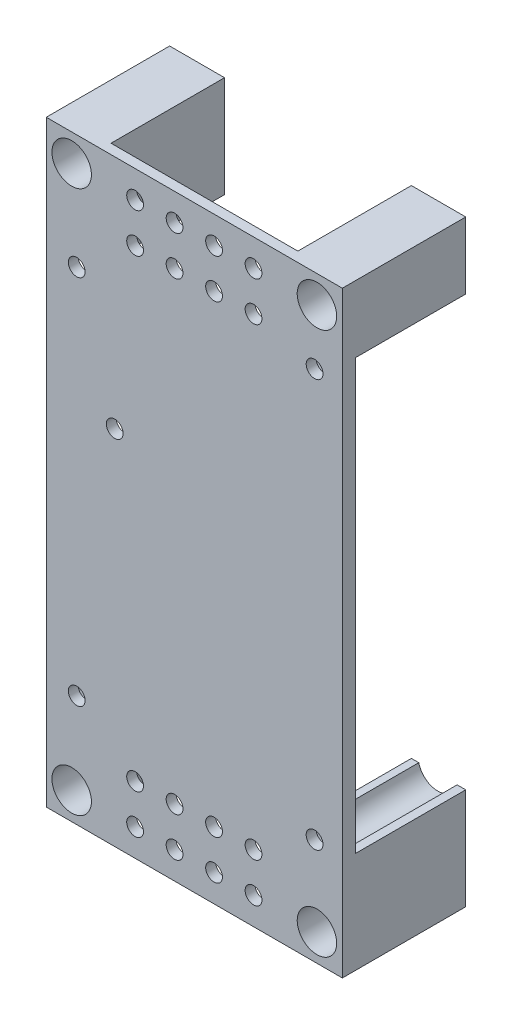
SolidWorks part; units mm, degrees
ref_plane "Plan de face" through (0, 0, 0) normal (0, 0, 1) x (1, 0, 0)
ref_plane "Plan de dessus" through (0, 0, 0) normal (0, 1, 0) x (1, 0, 0)
ref_plane "Plan de droite" through (0, 0, 0) normal (1, 0, 0) x (0, 0, -1)
sketch "Esquisse1" plane through (0, 0, 0) normal (0, 0, 1) x (1, 0, 0)
  line L5 (0.9187, 44.8704) -> (16.1486, 44.8704) construction
  line L8 (-13.8839, 67.0531) -> (-13.8839, -53.9979) construction
  line L9 (-43.8839, 67.0531) -> (16.1161, 67.0531)
  line L10 (-43.8839, 67.0531) -> (-43.8839, -53.9979)
  line L11 (-43.8839, -53.9979) -> (16.1161, -53.9979)
  line L12 (16.1161, 67.0531) -> (16.1161, -53.9979)
  line L13 (-43.8839, 6.5276) -> (16.1161, 6.5276) construction
  line L14 (-52.5801, -48.4724) -> (36.6857, -48.4724) construction
  line L15 (-38.8839, -50.2856) -> (-38.8839, -32.7452) construction
  circle A5 centre (-38.7333, -48.4724) radius 4
  circle A6 centre (10.9655, -48.4724) radius 4
  circle A7 centre (10.9655, 61.5276) radius 4
  circle A8 centre (-38.7333, 61.5276) radius 4
  line B0 (-37.7133, -31.3924) -> (-37.7133, 63.6939) construction
  line B1 (-37.7133, -31.3924) -> (13.3877, -31.3924) construction
  line B2 (-37.7133, 43.8476) -> (13.7913, 43.8476) construction
  line B3 (10.4867, 62.1293) -> (-37.7133, 62.1293) construction
  line B4 (10.4867, -32.5324) -> (10.4867, 66.0242) construction
  line B5 (3.5231, 50.0676) -> (21.137, 50.0676) construction
  line B6 (-13.6133, 62.1293) -> (-13.6133, 58.5502) construction
  line B7 (-48.2733, 19.324) -> (4.9867, 19.324) construction
  line B8 (-43.1133, 8.2967) -> (15.8867, 8.2967) construction
  circle B9 centre (10.4867, -32.5324) radius 1.7
  circle B10 centre (10.4867, 50.0676) radius 1.7
  circle B11 centre (-30.0133, 19.324) radius 1.7
  circle B12 centre (-37.7133, -31.3924) radius 1.7
  circle B13 centre (-37.7133, 43.8476) radius 1.7
  dimension "D4" = 60
  dimension "D5" = 17.08
  dimension "D1" = 55
  dimension "D2" = 121.051
  dimension "D3" = 25
  dimension "D6" = 1.02
sketch_block_instance "Bloc2-1"
sketch_block "Bloc2" parameters "D5"=4, "D1"=75.24, "D2"=48.2, "D3"=6.22, "D4"=1.14
extrude "Boss.-Extru.1" add sketch "Esquisse1" along normal blind 25
sketch "Esquisse2" plane through (16.1161, 0, 0) normal (1, 0, 0) x (0, 0, -1)
  line L0 (-25, 6.5276) -> (0, 6.5276) construction
  line L1 (-25, -53.9979) -> (-25, 67.0531) construction
  line L2 (0, -53.9979) -> (0, 67.0531) construction
  line L3 (-22.3, -67.4787) -> (-22.3, 79.6794) construction
  line L4 (-25, -33.4724) -> (0, -33.4724) construction
  line L5 (0, -33.4724) -> (-22.3, -33.4724)
  line L6 (-22.3, -33.4724) -> (-22.3, 46.5276)
  line L7 (0, -33.4724) -> (0, 46.5276) construction
  line L8 (0, 46.5276) -> (-22.3, 46.5276)
  point P14 (-22.3, 6.5276)
  dimension "D1" = 22.3
  dimension "D2" = 40
extrude "Enlèv. mat.-Extru.1" cut sketch "Esquisse2" against normal through all and the other way through all
sketch "Esquisse3" plane through (0, 0, 0) normal (0, 0, -1) x (-1, 0, 0)
  circle A0 centre (-10.4867, -32.5324) radius 4
  circle A1 centre (37.7133, -31.3924) radius 4
  circle A2 centre (-10.4867, 50.0676) radius 4
  circle A3 centre (37.7133, 43.8476) radius 4
extrude "Enlèv. mat.-Extru.2" cut sketch "Esquisse3" against normal blind 23
sketch "Esquisse4" plane through (0, -53.9979, 0) normal (0, -1, 0) x (1, 0, 0)
  line L1 (-32.76, 23) -> (5.0976, 23)
  line L2 (-32.76, 23) -> (-32.76, 0)
  line L3 (-32.76, 0) -> (5.0976, 0)
  line L4 (5.0976, 23) -> (5.0976, 0)
  line L5 (-43.8839, 0) -> (16.1161, 0) construction
extrude "Enlèv. mat.-Extru.3" cut sketch "Esquisse4" against normal blind 142
sketch "Esquisse5" plane through (0, 0, 25) normal (0, 0, 1) x (1, 0, 0)
  line L0 (-13.8839, 67.0531) -> (-13.8839, -53.9979) construction
  line L1 (16.1161, 67.0531) -> (-43.8839, 67.0531) construction
  line L2 (-43.8839, -53.9979) -> (16.1161, -53.9979) construction
  line L3 (10.9655, 61.5276) -> (-38.7333, 61.5276) construction
  line L4 (16.1161, 6.5276) -> (-43.8839, 6.5276) construction
  line L5 (16.1161, -53.9979) -> (16.1161, 67.0531) construction
  line L6 (-43.8839, 67.0531) -> (-43.8839, -53.9979) construction
  circle A0 centre (-9.8839, 61.5276) radius 1.7
  circle A1 centre (-1.8839, 61.5276) radius 1.7
  circle A2 centre (-1.8839, 53.5276) radius 1.7
  circle A3 centre (-9.8839, 53.5276) radius 1.7
  circle A4 centre (-17.8839, 53.5276) radius 1.7
  circle A5 centre (-25.8839, 53.5276) radius 1.7
  circle A6 centre (-25.8839, 61.5276) radius 1.7
  circle A7 centre (-17.8839, 61.5276) radius 1.7
  circle A8 centre (-17.8839, -48.4724) radius 1.7
  circle A9 centre (-25.8839, -48.4724) radius 1.7
  circle A10 centre (-25.8839, -40.4724) radius 1.7
  circle A11 centre (-17.8839, -40.4724) radius 1.7
  circle A12 centre (-9.8839, -40.4724) radius 1.7
  circle A13 centre (-1.8839, -40.4724) radius 1.7
  circle A14 centre (-1.8839, -48.4724) radius 1.7
  circle A15 centre (-9.8839, -48.4724) radius 1.7
  dimension "D1" = 4
  dimension "D2" = 2
  dimension "D3" = 2
extrude "Enlèv. mat.-Extru.4" cut sketch "Esquisse5" against normal blind 5
sketch "Esquisse6" plane through (0, 46.5276, 0) normal (0, -1, 0) x (1, 0, 0)
  line L1 (12.349, 22.3) -> (16.1161, 22.3)
  line L2 (12.349, 22.3) -> (12.349, 0)
  line L3 (12.349, 0) -> (16.1161, 0)
  line L4 (16.1161, 22.3) -> (16.1161, 0)
extrude "Enlèv. mat.-Extru.5" cut sketch "Esquisse6" against normal blind 7
